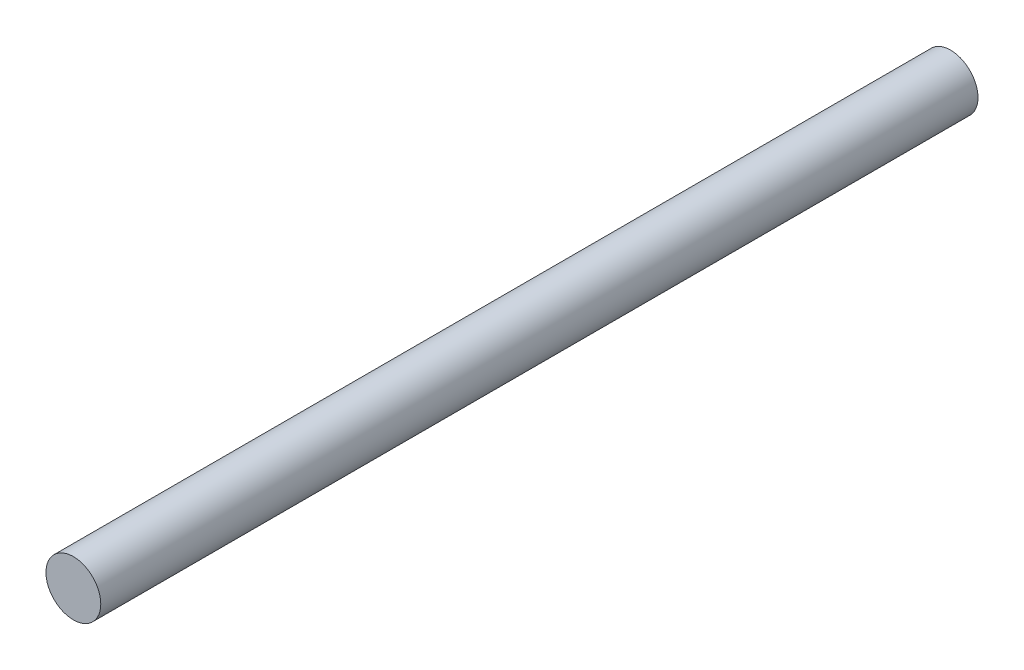
SolidWorks part; units mm, degrees
ref_plane "Front Plane" through (0, 0, 0) normal (0, 0, 1) x (1, 0, 0)
ref_plane "Top Plane" through (0, 0, 0) normal (0, 1, 0) x (1, 0, 0)
ref_plane "Right Plane" through (0, 0, 0) normal (1, 0, 0) x (0, 0, -1)
sketch "Sketch1" plane through (0, 0, 0) normal (0, 0, 1) x (1, 0, 0)
  circle A0 centre (0, 0) radius 19.05
  dimension "D1" = 38.1
extrude "Boss-Extrude2" add sketch "Sketch1" along normal blind 609.6 contours A0
sketch "Sketch2" plane through (0, 0, 0) normal (0, 0, -1) x (-1, 0, 0)
  line L0 (-19.05, 0) -> (19.05, 0)
  line L2 (-19.05, 0) -> (19.05, 0)
  line L3 (-19.05, 0) -> (-19.05, 0.0005)
  line L4 (-19.05, 0.0005) -> (19.05, 0.0005)
  line L5 (19.05, 0) -> (19.05, 0.0005)
  line L6 (-19.05, 0) -> (19.05, 0)
  line L7 (-19.05, 0) -> (-19.05, -0.0005)
  line L8 (-19.05, -0.0005) -> (19.05, -0.0005)
  line L9 (19.05, 0) -> (19.05, -0.0005)
  circle A0 centre (0, 0) radius 19.05 construction
  circle M3 centre (0, 0) radius 19.05
  dimension "D1" = 0.0005
  dimension "D2" = 0.0005
extrude "Cut-Extrude1" cut sketch "Sketch2" against normal blind 50.8 contours L4 L0 M3
sketch "Sketch5" plane through (0, 0, 0) normal (0, 0, -1) x (-1, 0, 0)
  line L1 (-19.05, 0) -> (19.05, 0)
  line L2 (-19.05, 0) -> (-19.05, -0.0005)
  line L3 (-19.05, -0.0005) -> (19.05, -0.0005)
  line L4 (19.05, 0) -> (19.05, -0.0005)
  dimension "D1" = 0.0005
extrude "Cut-Extrude6" cut sketch "Sketch5" against normal blind 50.8 contours L2 L1 L4 L3
